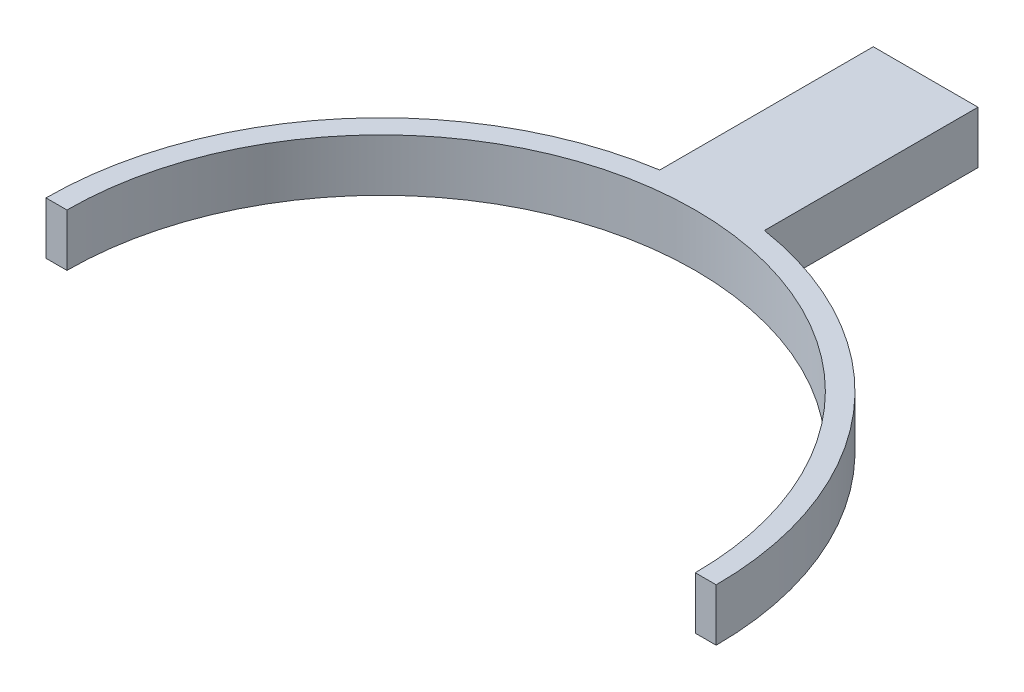
SolidWorks part; units mm, degrees
ref_plane "前视基准面" through (0, 0, 0) normal (0, 0, 1) x (1, 0, 0)
ref_plane "上视基准面" through (0, 0, 0) normal (0, 1, 0) x (1, 0, 0)
ref_plane "右视基准面" through (0, 0, 0) normal (1, 0, 0) x (0, 0, -1)
sketch "草图1" plane through (0, 0, 0) normal (0, 1, 0) x (1, 0, 0)
  line L0 (-32, 0) -> (-30, 0)
  line L1 (30, 0) -> (32, 0)
  arc A0 (30, 0) -> (-30, 0) centre (0, 0) ccw
  arc A1 (32, 0) -> (-32, 0) centre (0, 0) ccw
extrude "凸台-拉伸1" add sketch "草图1" along normal blind 5
sketch "草图2" plane through (0, 0, 0) normal (0, 1, 0) x (1, 0, 0)
  line L0 (0, 32) -> (0, 52)
  line L1 (0, 52) -> (5, 52)
  line L2 (5, 52) -> (5, 31)
  line L3 (5, 31) -> (-5, 31)
  line L4 (-5, 31) -> (-5, 52)
  line L5 (-5, 52) -> (0, 52)
  arc A0 (32, 0) -> (-32, 0) centre (0, 0) ccw construction
extrude "凸台-拉伸2" add sketch "草图2" along normal blind 5
